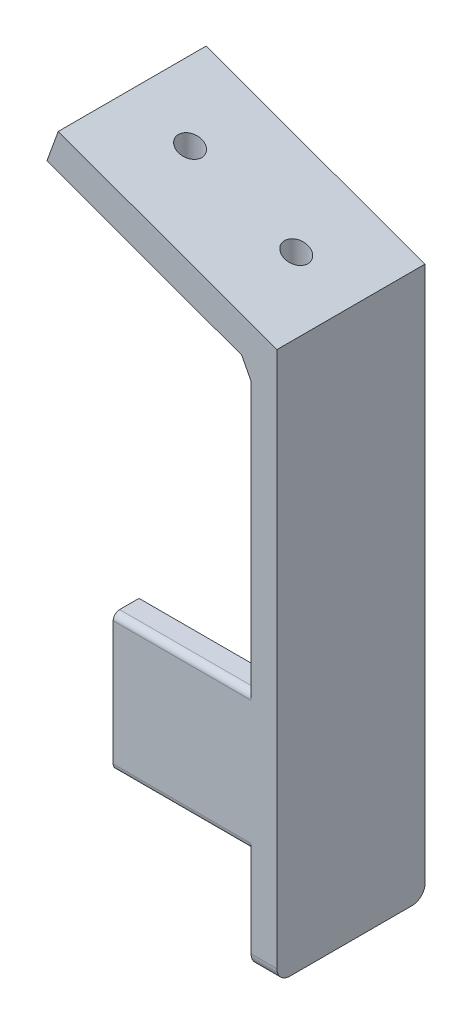
SolidWorks part; units mm, degrees
ref_plane "Plan de face" through (0, 0, 0) normal (0, 0, 1) x (1, 0, 0)
ref_plane "Plan de dessus" through (0, 0, 0) normal (0, 1, 0) x (1, 0, 0)
ref_plane "Plan de droite" through (0, 0, 0) normal (1, 0, 0) x (0, 0, -1)
sketch "Esquisse1" plane through (0, 0, 0) normal (0, 0, 1) x (1, 0, 0)
  line L0 (0, 26.549) -> (0, -58.451)
  line L1 (0, -58.451) -> (-4, -58.451)
  line L2 (-4, -58.451) -> (-4, 26.549)
  line L8 (-4, 26.549) -> (0, 26.549)
extrude "Boss.-Extru.1" add sketch "Esquisse1" along normal blind 22.93
sketch "Esquisse2" plane through (0, 0, 22.93) normal (0, 0, 1) x (1, 0, 0)
  line L4 (-33.8506, 38.8696) -> (0, 26.549)
  line L5 (0, 26.549) -> (0, 22.549)
  line L6 (0, -58.451) -> (0, 26.549) construction
  line L7 (0, 22.549) -> (-4, 22.549)
  line L8 (-4, 26.549) -> (-4, -58.451) construction
  line L9 (-4, 22.549) -> (-35.6041, 34.052)
  line L10 (-35.6041, 34.052) -> (-33.8506, 38.8696)
extrude "Boss.-Extru.5" add sketch "Esquisse2" against normal blind 22.9
sketch "Esquisse5" plane through (0, 0, 22.93) normal (0, 0, 1) x (1, 0, 0)
  line L1 (0, -58.451) -> (0, 26.549) construction
  line L2 (0, -21.471) -> (-25.35, -21.471)
  line L5 (-25.35, -21.471) -> (-25.35, -42.6526)
  line L6 (-25.35, -42.6526) -> (0, -42.6526)
  line L7 (0, -42.6526) -> (0, -21.471)
extrude "Boss.-Extru.6" add sketch "Esquisse5" against normal blind 4
sketch "Esquisse7" plane through (0, 0, 0) normal (1, 0, 0) x (0, 0, -1)
  line L0 (0, -32.571) -> (0, -21.471)
  line L1 (0, 26.549) -> (0, -58.451) construction
  line L2 (-22.93, -42.6526) -> (-22.93, -21.471) construction
  line L4 (0, -21.471) -> (0, -32.571) construction
  line L6 (0, -32.571) -> (-1.98, -32.571)
  line L7 (-1.98, -32.571) -> (-1.98, -21.471)
  line L8 (-1.98, -21.471) -> (0, -21.471)
fillet "Congé1" radius 2 2 edges at (-2, -58.451, 22.93) (-2, -58.451, 0)
fillet "Congé5" radius 1 2 edges at (-14.675, -42.6526, 22.93) (-14.675, -21.471, 22.93)
sketch "Esquisse9" plane through (0, 0, 0) normal (0, 1, 0) x (1, 0, 0)
  line L0 (-16.9674, -11.4391) -> (0, -11.48) construction
  line L1 (-16.9674, -11.4391) -> (-32.9012, -11.4391) construction
  line L2 (0, -22.93) -> (0, -0.03) construction
  circle A0 centre (-24.9343, -11.4391) radius 1.8
  circle A1 centre (-8.4837, -11.4595) radius 1.8
extrude "Enlèv. mat.-Extru.1" cut sketch "Esquisse9" along normal blind 58
sketch "Esquisse10" plane through (-4, 0, 0) normal (-1, 0, 0) x (0, 0, 1)
  line L0 (5.5645, 13.239) -> (17.7163, 13.239) construction
  text T0 "R" font "Century Gothic" height 5
extrude "Boss.-Extru.8" add sketch "Esquisse10" along normal blind 1
sketch "Esquisse11" plane through (0, 0, 22.93) normal (0, 0, 1) x (1, 0, 0)
  line L0 (-5.4528, 23.0778) -> (-4, 20.2984)
  line L1 (-35.6041, 34.052) -> (-4, 22.549) construction
  line L2 (-4, 22.549) -> (-4, -22.471) construction
  line L3 (-4, 20.2984) -> (-0.6592, 23.0778)
  line L4 (-0.6592, 23.0778) -> (-5.4528, 23.0778)
extrude "Boss.-Extru.9" add sketch "Esquisse11" against normal blind 22.9
